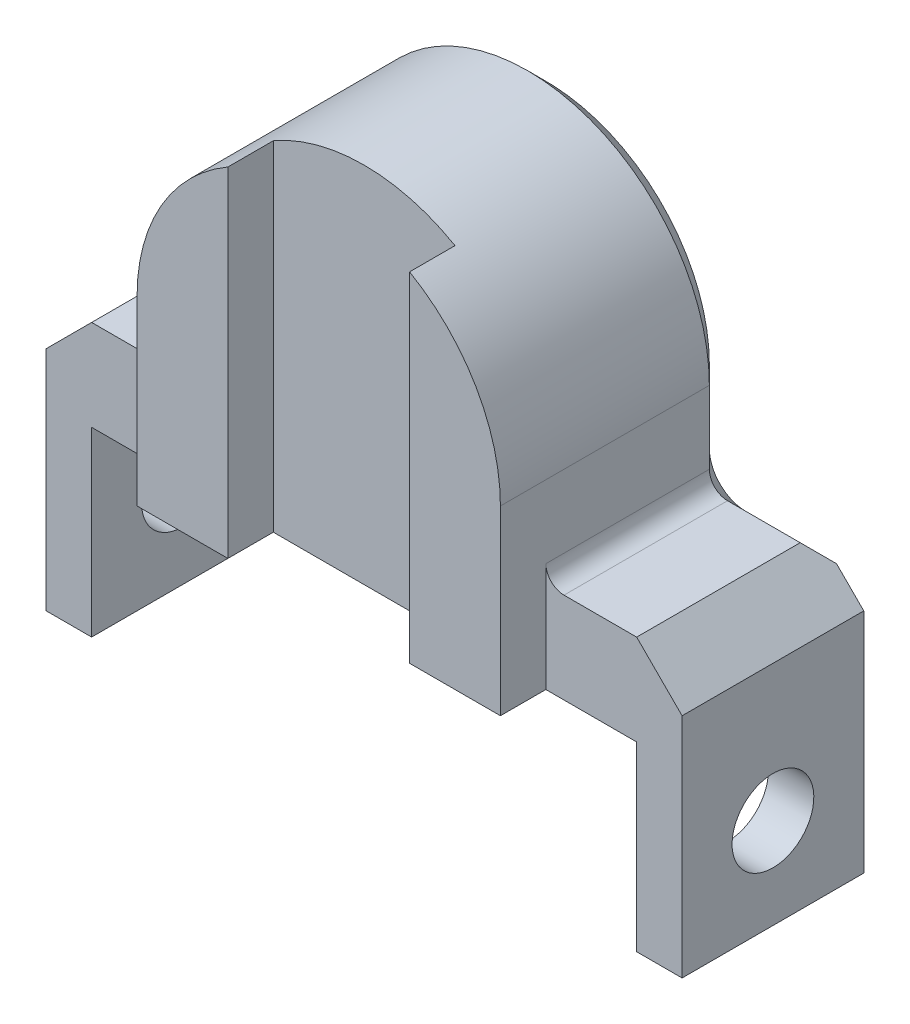
SolidWorks part; units mm, degrees
ref_plane "前视基准面" through (0, 0, 0) normal (0, 0, 1) x (1, 0, 0)
ref_plane "上视基准面" through (0, 0, 0) normal (0, 1, 0) x (1, 0, 0)
ref_plane "右视基准面" through (0, 0, 0) normal (1, 0, 0) x (0, 0, -1)
sketch "草图1" plane through (0, 0, 0) normal (0, 0, 1) x (1, 0, 0)
  line L0 (-30, 0) -> (30, 0)
  line L1 (30, 0) -> (30, -20)
  line L2 (30, -20) -> (35, -20)
  line L3 (35, -20) -> (35, 10)
  line L4 (20, 20) -> (0, 20) construction
  line L6 (0, 20) -> (0, 40) construction
  line L8 (-35, -20) -> (-35, 10)
  line L9 (-30, -20) -> (-35, -20)
  line L10 (-30, 0) -> (-30, -20)
  line L11 (20, 20) -> (20, 10)
  line L12 (20, 10) -> (35, 10)
  line L13 (-20, 10) -> (-35, 10)
  line L14 (-20, 20) -> (-20, 10)
  arc A0 (20, 20) -> (-20, 20) centre (0, 20) ccw
  point P14 (0, 0)
extrude "凸台-拉伸1" add sketch "草图1" along normal mid plane 20
sketch "草图2" plane through (-35, 0, 0) normal (-1, 0, 0) x (0, 0, 1)
  line L0 (-10, -20) -> (0, -20) construction
  line L1 (10, -20) -> (-10, -20) construction
  line L2 (0, -20) -> (0, -10) construction
  circle A0 centre (0, -10) radius 4.5
extrude "切除-拉伸1" cut sketch "草图2" against normal through all
chamfer "倒角3" distance 5 angle 45 2 edges at (-35, 10, 0) (35, 10, 0)
fillet "圆角2" radius 2 2 edges at (-20, 10, 0) (20, 10, 0)
chamfer "倒角5" distance 2 angle 45 7 edges at (26, 10, -10) (-26, 10, -10) (20.5858, 10.5858, -10) (-20.5858, 10.5858, -10) (20, 16, -10) (-20, 16, -10) (0, 40, -10)
sketch "草图3" plane through (0, 0, 10) normal (0, 0, 1) x (1, 0, 0)
  line L0 (0, 0) -> (0, 20) construction
  line L1 (20, 0) -> (10, 0)
  line L2 (-30, 0) -> (30, 0) construction
  line L3 (-10, 0) -> (-10, 37.3205)
  line L4 (-20, 20) -> (-20, 0)
  line L5 (-20, 0) -> (-10, 0)
  line L6 (20, 20) -> (20, 0)
  line L7 (10, 0) -> (10, 37.3205)
  arc A0 (-10, 37.3205) -> (-20, 20) centre (0, 20) ccw
  arc A1 (10, 37.3205) -> (20, 20) centre (0, 20) cw
extrude "凸台-拉伸2" add sketch "草图3" along normal blind 5
